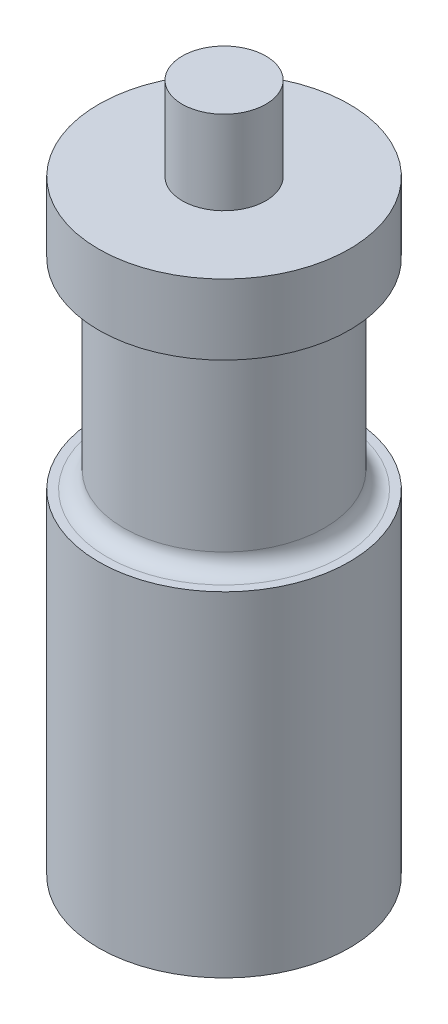
SolidWorks part; units mm, degrees
ref_plane "Front" through (0, 0, 0) normal (0, 0, 1) x (1, 0, 0)
ref_plane "Top" through (0, 0, 0) normal (0, 1, 0) x (1, 0, 0)
ref_plane "Right" through (0, 0, 0) normal (1, 0, 0) x (0, 0, -1)
sketch "Sketch1" plane through (0, 0, 0) normal (0, 0, 1) x (1, 0, 0)
  line L0 (0, 25.2693) -> (0, -27.3365) construction
  line L2 (0, 0) -> (-7.5, 0)
  line L3 (0, 0) -> (0, -20)
  line L4 (0, -20) -> (-7.5, -20)
  line L5 (-7.5, 0) -> (-7.5, -20)
  line L6 (0, 0) -> (-6, 0)
  line L7 (0, 0) -> (0, 12)
  line L8 (0, 12) -> (-6, 12)
  line L9 (-6, 0) -> (-6, 12)
  line L10 (0, 12) -> (-7.5, 12)
  line L11 (0, 12) -> (0, 16.2)
  line L12 (0, 16.2) -> (-7.5, 16.2)
  line L13 (-7.5, 12) -> (-7.5, 16.2)
  line L14 (0, 16.2) -> (-2.5, 16.2)
  line L15 (0, 16.2) -> (0, 21.2)
  line L16 (0, 21.2) -> (-2.5, 21.2)
  line L17 (-2.5, 16.2) -> (-2.5, 21.2)
  dimension "D1" = 15
  dimension "D2" = 20
  dimension "D3" = 12
  dimension "D4" = 12
  dimension "D5" = 15
  dimension "D6" = 4.2
  dimension "D7" = 5
  dimension "D8" = 5
revolve "Revolve1" add sketch "Sketch1" angle 360 about L0
fillet "Fillet1" radius 1 2 edges at (0, 12, 6) (0, 0, 6)
